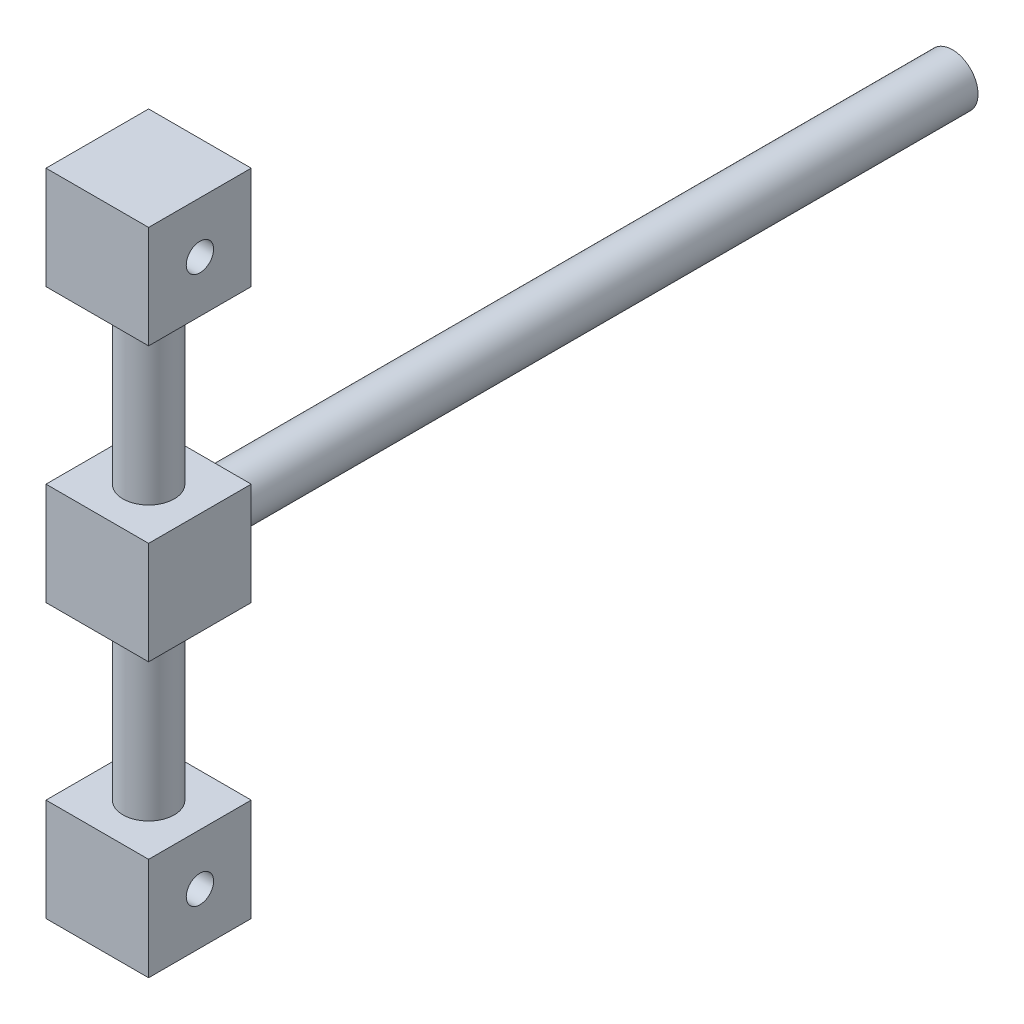
SolidWorks part; units mm, degrees
ref_plane "前视基准面" through (0, 0, 0) normal (0, 0, 1) x (1, 0, 0)
ref_plane "上视基准面" through (0, 0, 0) normal (0, 1, 0) x (1, 0, 0)
ref_plane "右视基准面" through (0, 0, 0) normal (1, 0, 0) x (0, 0, -1)
sketch "草图1" plane through (0, 0, 0) normal (0, 0, 1) x (1, 0, 0)
  line L1 (15, -15) -> (-15, -15)
  line L2 (15, -15) -> (15, 15)
  line L3 (15, 15) -> (-15, 15)
  line L4 (-15, -15) -> (-15, 15)
  line L5 (15, -15) -> (-15, 15) construction
  line L6 (15, 15) -> (-15, -15) construction
  point P0 (0, 0)
  dimension "D1" = 30
extrude "凸台-拉伸1" add sketch "草图1" along normal blind 30
sketch "草图2" plane through (0, 0, 0) normal (0, 0, -1) x (-1, 0, 0)
  circle A0 centre (0, 0) radius 7.5
  dimension "D1" = 15
extrude "凸台-拉伸2" add sketch "草图2" along normal blind 220
sketch "草图3" plane through (0, -15, 0) normal (0, -1, 0) x (1, 0, 0)
  line L0 (-15, 0) -> (15, 30) construction
  line L1 (15, 0) -> (-15, 30) construction
  circle A0 centre (0, 15) radius 7.5
  dimension "D1" = 15
extrude "凸台-拉伸3" add sketch "草图3" along normal blind 50
sketch "草图4" plane through (0, -65, 0) normal (0, -1, 0) x (1, 0, 0)
  line L1 (-15, 30) -> (15, 30)
  line L2 (-15, 30) -> (-15, 0)
  line L3 (-15, 0) -> (15, 0)
  line L4 (15, 30) -> (15, 0)
  line L5 (-15, 30) -> (15, 0) construction
  line L6 (-15, 0) -> (15, 30) construction
  point P0 (0, 15)
extrude "凸台-拉伸4" add sketch "草图4" along normal blind 30
sketch "草图5" plane through (-15, 0, 0) normal (-1, 0, 0) x (0, 0, 1)
  line L0 (0, -95) -> (30, -65) construction
  circle A0 centre (15, -80) radius 4
  dimension "D1" = 8
extrude "切除-拉伸1" cut sketch "草图5" against normal through all
mirror "镜向1" about plane through (0, 0, 0) normal (0, 1, 0) of "切除-拉伸1", "凸台-拉伸3", "凸台-拉伸4"
